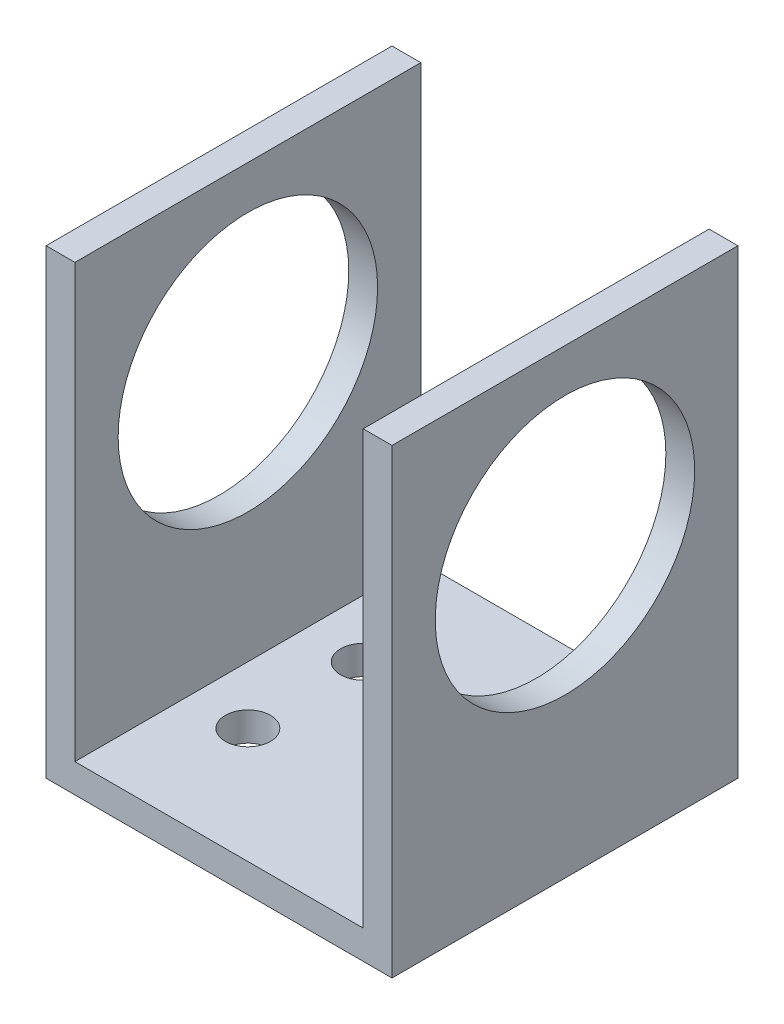
SolidWorks part; units mm, degrees
ref_plane "Front Plane" through (0, 0, 0) normal (0, 0, 1) x (1, 0, 0)
ref_plane "Top Plane" through (0, 0, 0) normal (0, 1, 0) x (1, 0, 0)
ref_plane "Right Plane" through (0, 0, 0) normal (1, 0, 0) x (0, 0, -1)
sketch "Sketch1" plane through (0, 0, 0) normal (0, 0, 1) x (1, 0, 0)
  line L0 (0, 0) -> (0, 50.8)
  line L1 (0, 50.8) -> (3.175, 50.8)
  line L2 (3.175, 50.8) -> (3.175, 3.175)
  line L3 (3.175, 3.175) -> (34.925, 3.175)
  line L4 (34.925, 3.175) -> (34.925, 50.8)
  line L5 (34.925, 50.8) -> (38.1, 50.8)
  line L6 (38.1, 50.8) -> (38.1, 0)
  line L7 (38.1, 0) -> (0, 0)
  line L8 (19.05, 0) -> (19.05, 3.175) construction
  dimension "D1" = 50.8
  dimension "D2" = 38.1
  dimension "D3" = 3.175
extrude "Boss-Extrude1" add sketch "Sketch1" along normal blind 38.1
sketch "Sketch2" plane through (38.1, 0, 0) normal (1, 0, 0) x (0, 0, -1)
  line L0 (-19.05, 0) -> (-19.05, 31.75) construction
  line L1 (-38.1, 0) -> (0, 0) construction
  circle A0 centre (-19.05, 31.75) radius 14.2875
  dimension "D1" = 28.575
  dimension "D2" = 31.75
extrude "Cut-Extrude1" cut sketch "Sketch2" against normal through all
sketch "Sketch3" plane through (0, 3.175, 0) normal (0, 1, 0) x (1, 0, 0)
  line L0 (3.175, -38.1) -> (3.175, 0) construction
  line L1 (3.175, -6.35) -> (34.925, -6.35) construction
  line L2 (3.175, -6.35) -> (3.175, -31.75) construction
  line L3 (3.175, -31.75) -> (34.925, -31.75) construction
  line L4 (34.925, -6.35) -> (34.925, -31.75) construction
  line L5 (34.925, -38.1) -> (34.925, 0) construction
  line L6 (34.925, 0) -> (3.175, 0) construction
  line L8 (9.525, -12.7) -> (28.575, -12.7) construction
  line L9 (9.525, -12.7) -> (9.525, -25.4) construction
  line L10 (9.525, -25.4) -> (28.575, -25.4) construction
  line L11 (28.575, -12.7) -> (28.575, -25.4) construction
  line L12 (9.525, -12.7) -> (28.575, -25.4) construction
  line L13 (9.525, -25.4) -> (28.575, -12.7) construction
  circle A0 centre (9.525, -12.7) radius 2.4892
  circle A1 centre (9.525, -25.4) radius 2.4892
  circle A2 centre (28.575, -25.4) radius 2.4892
  circle A3 centre (28.575, -12.7) radius 2.4892
  point P10 (19.05, -19.05)
  point P15 (34.925, -19.05)
  dimension "D7" = 4.9784
  dimension "D1" = 25.4
  dimension "D2" = 6.35
  dimension "D3" = 6.35
  dimension "D4" = 6.35
  dimension "D5" = 6.35
  dimension "D6" = 6.35
extrude "Cut-Extrude2" cut sketch "Sketch3" against normal through all
